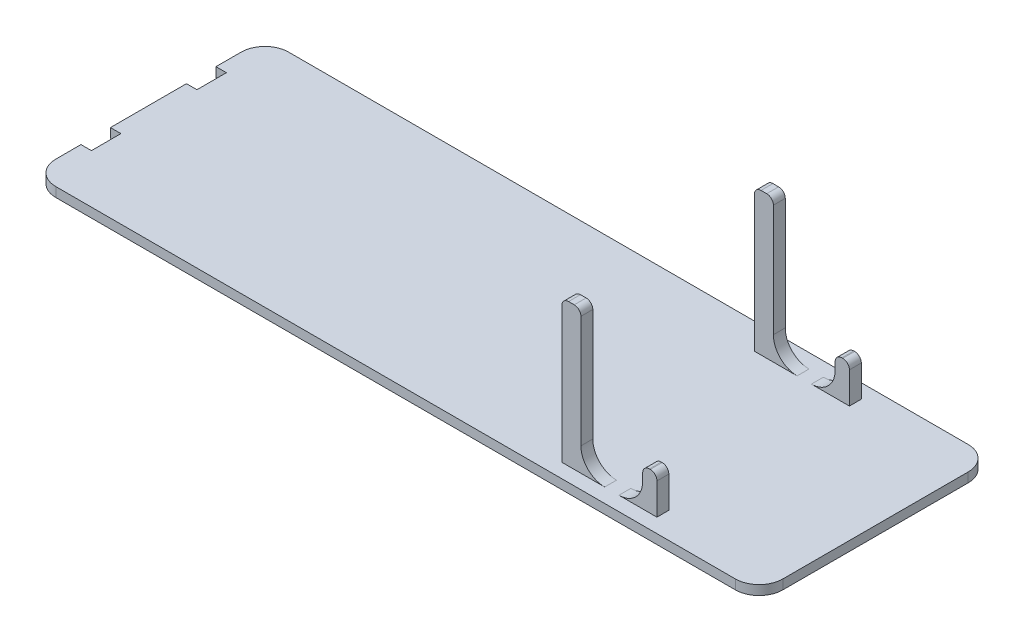
SolidWorks part; units mm, degrees
ref_plane "Спереди" through (0, 0, 0) normal (0, 0, 1) x (1, 0, 0)
ref_plane "Сверху" through (0, 0, 0) normal (0, 1, 0) x (1, 0, 0)
ref_plane "Справа" through (0, 0, 0) normal (1, 0, 0) x (0, 0, -1)
sketch "Эскиз1" plane through (0, 0, 0) normal (0, 1, 0) x (1, 0, 0)
  line L0 (-76.5, 0) -> (-74.5, 0) construction
  line L1 (-71.5, 24.5) -> (71.5, 24.5)
  line L2 (-76.5, 19.5) -> (-76.5, -19.5)
  line L3 (-71.5, -24.5) -> (0, -24.5)
  line L4 (76.5, 19.5) -> (76.5, 15.5)
  line L5 (0, -24.5) -> (0, 24.5) construction
  line L6 (17.5, 0) -> (19.5, 0) construction
  line L7 (-74.5, 0) -> (-29.5, 0) construction
  line L8 (-74.5, 0) -> (-74.5, 17.5)
  line L9 (-29.5, 0) -> (-29.5, 22.5)
  line L10 (-29.5, 22.5) -> (-71.5, 22.5)
  line L11 (-29.5, 24.5) -> (-29.5, 22.5) construction
  line L12 (-29.5, 0) -> (-27.5, 0) construction
  line L13 (-27.5, 0) -> (17.5, 0) construction
  line L14 (19.5, 0) -> (64.5, 0) construction
  line L15 (-27.5, 0) -> (-27.5, 22.5)
  line L16 (-27.5, 22.5) -> (17.5, 22.5)
  line L17 (17.5, 22.5) -> (17.5, 0)
  line L18 (19.5, 0) -> (19.5, 17.5)
  line L19 (31.5, 22.5) -> (52.5, 22.5)
  line L20 (64.5, 17.5) -> (64.5, 0)
  line L21 (75.5, 14.5) -> (74.5, 14.5)
  line L22 (66.5, 0) -> (66.5, 20)
  line L23 (68.5, 22) -> (71.5, 22)
  line L24 (73.5, 20) -> (73.5, 15.5)
  line L25 (64.5, 0) -> (66.5, 0) construction
  line L26 (-74.5, 0) -> (-76.5, 0)
  line L27 (-29.5, 0) -> (-27.5, 0)
  line L28 (17.5, 0) -> (19.5, 0)
  line L29 (64.5, 0) -> (66.5, 0)
  line L30 (0, -24.5) -> (71.5, -24.5)
  line L31 (76.5, -19.5) -> (76.5, 15.5)
  line L32 (-74.5, 19.5045) -> (-74.5, 17.5)
  line L33 (19.5, 17.5) -> (29.5, 17.5)
  line L34 (31.5, 19.5) -> (31.5, 22.5)
  line L35 (64.5, 17.5) -> (54.5, 17.5)
  line L36 (52.5, 19.5) -> (52.5, 22.5)
  line L37 (66.5, 0) -> (66.5, 22)
  line L38 (66.5, 22) -> (68.5, 22)
  line L39 (-27.5, 24.5) -> (-27.5, 22.5) construction
  line L40 (42, 22.5) -> (42, 24.5) construction
  arc A1 (71.5, 24.5) -> (76.5, 19.5) centre (71.5, 19.5) cw
  arc A2 (-71.5, -24.5) -> (-76.5, -19.5) centre (-71.5, -19.5) cw
  arc A3 (-76.5, 19.5) -> (-71.5, 24.5) centre (-71.5, 19.5) cw
  arc A4 (-71.5, 22.5) -> (-74.5, 19.5045) centre (-71.5, 19.5) ccw
  arc A5 (76.5, 15.5) -> (75.5, 14.5) centre (75.5, 15.5) cw
  arc A6 (74.5, 14.5) -> (73.5, 15.5) centre (74.5, 15.5) cw
  arc A7 (76.5, -19.5) -> (71.5, -24.5) centre (71.5, -19.5) cw
  arc A8 (71.5, 22) -> (73.5, 20) centre (71.5, 20) cw
  arc A9 (66.5, 20) -> (68.5, 22) centre (68.5, 20) cw
  arc A10 (54.5, 17.5) -> (52.5, 19.5) centre (54.5, 19.5) cw
  arc A11 (29.5, 17.5) -> (31.5, 19.5) centre (29.5, 19.5) ccw
  point P0 (0, 0)
  point P8 (76.5, 24.5)
  point P12 (-76.5, -24.5)
  point P15 (-76.5, 24.5)
  point P39 (76.5, 14.5)
  point P42 (74.5, 14.5)
  point P49 (74.5, 21.5)
  point P55 (66.5, 0)
  point P59 (52.5, 17.5)
  point P62 (31.5, 17.5)
  dimension "D3" = 5
  dimension "D4" = 5
  dimension "D15" = 1
  dimension "D19" = 2
  dimension "D20" = 2
  dimension "D24" = 2
  dimension "D1" = 153
  dimension "D2" = 49
  dimension "D5" = 2
  dimension "D6" = 45
  dimension "D7" = 2
  dimension "D8" = 2
  dimension "D9" = 45
  dimension "D10" = 2
  dimension "D11" = 45
  dimension "D12" = 2
  dimension "D13" = 7
  dimension "D14" = 2
  dimension "D16" = 12
  dimension "D17" = 5
  dimension "D18" = 12
  dimension "D21" = 22
  dimension "D22" = 2
  dimension "D23" = 2
extrude "Бобышка-Вытянуть3" add sketch "Эскиз1" against normal blind 2 separate body
sketch "Эскиз4" plane through (0, 0, 0) normal (0, 1, 0) x (1, 0, 0)
  line L0 (-76.5, 0) -> (-76.5, -8) construction
  line L1 (-76.5, 19.5) -> (-76.5, -19.5) construction
  line L3 (-76.5, -8) -> (-74.3, -8)
  line L4 (-76.5, -8) -> (-76.5, -14.2)
  line L5 (-76.5, -14.2) -> (-74.3, -14.2)
  line L6 (-74.3, -8) -> (-74.3, -14.2)
  dimension "D1" = 8
  dimension "D2" = 6.2
  dimension "D3" = 2.2
extrude "Вырез-Вытянуть2" cut sketch "Эскиз4" against normal through all both and the other way through all
mirror "Зеркальное отражение3" about plane through (0, 0, 0) normal (0, 0, 1) of "Вырез-Вытянуть2"
ref_plane "Плоскость1" through (0, 0, -21.5) normal (0, 0, -1) x (-1, 0, 0)
sketch "Эскиз5" plane through (0, 0, -21.5) normal (0, 0, -1) x (-1, 0, 0)
  line L0 (-42, 0) -> (-42, -2) construction
  line L1 (71.5, -2) -> (-71.5, -2) construction
sketch "Эскиз6" plane through (0, 0, -21.5) normal (0, 0, -1) x (-1, 0, 0)
  line L0 (-42, 0) -> (-49, 0)
  line L1 (0, 0) -> (-71.5, 0) construction
  line L2 (-42, 0) -> (-36, 0)
  line L3 (-49, 0) -> (-49, 6.6)
  line L4 (-50.4, 8) -> (-50.6, 8)
  line L5 (-52, 6.6) -> (-52, 0)
  line L6 (-36, 0) -> (-36, 28.6)
  line L7 (-34.6, 30) -> (-33.4, 30)
  line L8 (-32, 28.6) -> (-32, 0)
  line L9 (-36, 0) -> (-32, 0)
  line L10 (-49, 0) -> (-52, 0)
  arc A0 (-50.6, 8) -> (-52, 6.6) centre (-50.6, 6.6) ccw
  arc A1 (-50.4, 8) -> (-49, 6.6) centre (-50.4, 6.6) cw
  arc A2 (-32, 28.6) -> (-33.4, 30) centre (-33.4, 28.6) ccw
  arc A3 (-36, 28.6) -> (-34.6, 30) centre (-34.6, 28.6) cw
  point P14 (-52, 8)
  point P17 (-49, 8)
  point P20 (-32, 30)
  point P23 (-36, 30)
  dimension "D9" = 1.4
  dimension "D10" = 1.4
  dimension "D1" = 7
  dimension "D2" = 6
  dimension "D3" = 30
  dimension "D4" = 30
  dimension "D5" = 4
  dimension "D6" = 3
  dimension "D7" = 8
  dimension "D8" = 8
extrude "Бобышка-Вытянуть4" add sketch "Эскиз6" against normal blind 2.5 contours A3 L6 L9 L8 A2 L7 | A1 L4 A0 L5 L10 L3
mirror "Зеркальное отражение4" about plane through (0, 0, 0) normal (0, 0, 1) of "Бобышка-Вытянуть4"
fillet "Скругление1" radius 5 4 edges at (36, 0, 20.25) (49, 0, -20.25) (36, 0, -20.25) (49, 0, 20.25)
